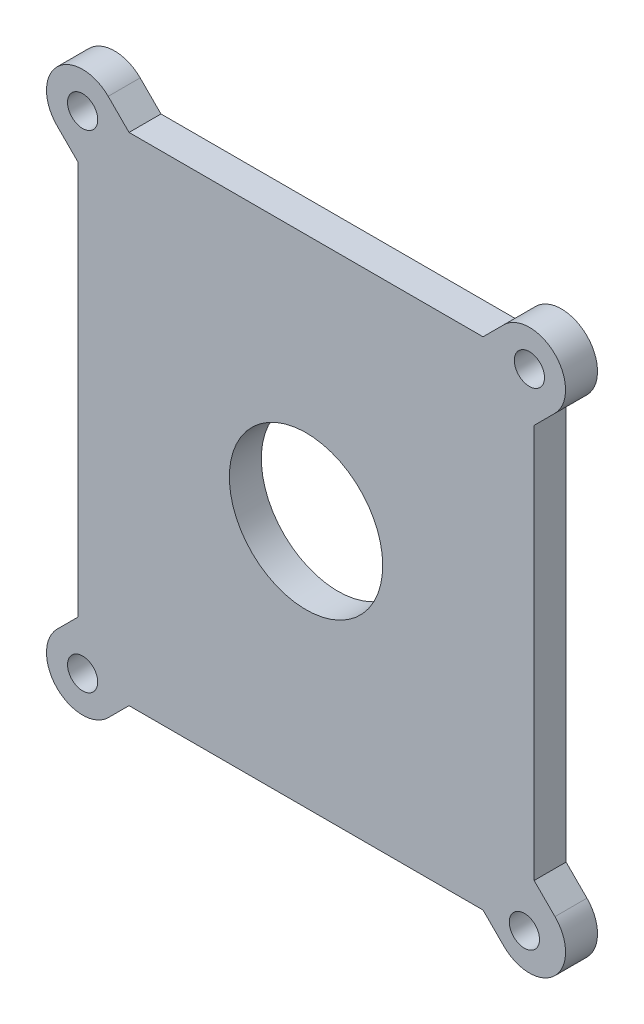
SolidWorks part; units mm, degrees
material "Acrylic (Medium-high impact)"
ref_plane "X-Y Datum" through (0, 0, 0) normal (0, 0, 1) x (1, 0, 0)
ref_plane "X-Z Datum" through (0, 0, 0) normal (0, 1, 0) x (1, 0, 0)
ref_plane "Y-Z Datum" through (0, 0, 0) normal (1, 0, 0) x (0, 0, -1)
sketch "Sketch1" plane through (0, 0, 0) normal (0, 0, 1) x (1, 0, 0)
  line L0 (33.9979, 36.9951) -> (33.9979, -36.9951)
  line L1 (-33.9979, -36.9951) -> (33.9979, -36.9951)
  line L2 (-33.9979, -36.9951) -> (-33.9979, 36.9951)
  line L3 (-33.9979, 36.9951) -> (33.9979, 36.9951)
  line L5 (-33.9979, -36.9951) -> (33.9979, 36.9951) construction
  line L6 (-33.9979, 36.9951) -> (33.9979, -36.9951) construction
  line L7 (26.3779, -36.9951) -> (26.3779, -29.3751)
  line L9 (26.3779, -29.3751) -> (33.9979, -29.3751)
  line L13 (26.3779, -36.9951) -> (29.4839, -40.1011)
  line L14 (33.9979, -29.3751) -> (37.1039, -32.4811)
  line L15 (33.9264, -36.9951) -> (33.9979, -36.9236)
  arc A1 (29.4839, -40.1011) -> (37.1039, -32.4811) centre (33.2939, -36.2911) ccw
  circle A2 centre (0, 0) radius 11.43
  point P0 (0, 0)
  dimension "D3" = 22.86
  dimension "D1" = 7.62
  dimension "D2" = 7.62
extrude "Boss-Extrude1" add sketch "Sketch1" along normal blind 4.7625
mirror "Mirror1" about plane through (0, 0, 0) normal (0, 1, 0) of "Boss-Extrude1"
mirror "Mirror2" about plane through (0, 0, 0) normal (1, 0, 0) of "Mirror1", "Boss-Extrude1"
sketch "Sketch3" plane through (0, 0, 4.7625) normal (0, 0, 1) x (1, 0, 0)
  line L0 (0, 0) -> (29.1039, -32.956) construction
  line L1 (29.1039, -32.956) -> (32.5472, -36.5867) construction
  line L2 (32.5472, -36.5867) -> (37.0392, -41.3231) construction
  circle A0 centre (32.5472, -36.5867) radius 2.9591
  circle A1 centre (32.5472, -36.5867) radius 5.4991
sketch "Sketch7" plane through (0, 0, 4.7625) normal (0, 0, 1) x (1, 0, 0)
  point P0 (32.5472, -36.5867)
  point P1 (-33.2939, -36.2911)
  point P3 (33.2939, 36.2911)
  point P5 (-33.2939, 36.2911)
hole_wizard "M4 Clearance Hole2" positions "Sketch8" profile "Sketch9" hole size "M4" standard "ANSI Metric" end condition through all
sketch "Sketch8" plane through (0, 0, 4.7625) normal (0, 0, 1) x (1, 0, 0)
  point P0 (-33.2939, 36.2911)
  point P3 (33.2939, 36.2911)
  point P6 (32.5472, -36.5867)
  point P9 (-33.2939, -36.2911)
sketch "Sketch9" plane through (-33.2939, 36.2911, 4.7625) normal (1, 0, 0) x (0, -1, 0)
  line L0 (0, 0) -> (0, 4.7625)
  line L1 (0, 4.7625) -> (2.25, 4.7625)
  line L2 (2.25, 4.7625) -> (2.25, 0)
  line L5 (2.25, 0) -> (0, 0)
  line L11 (0, -6.35) -> (0, 107.95) construction
  dimension "Thru Hole Dia." = 4.5
  dimension "Thru Hole Depth" = 4.7625
